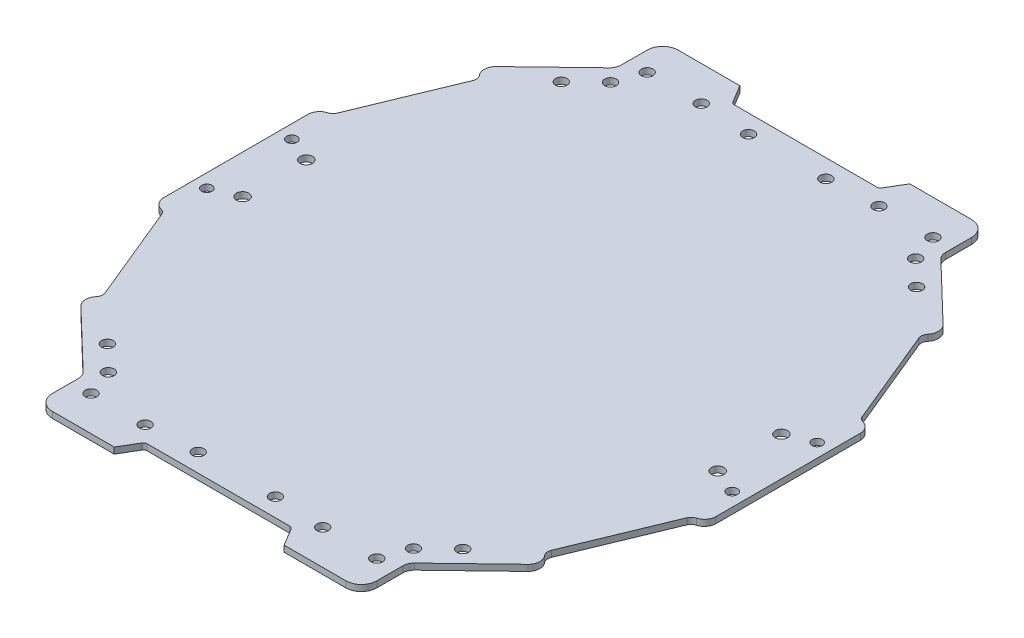
SolidWorks part; units mm, degrees
ref_plane "Front Plane" through (0, 0, 0) normal (0, 0, 1) x (1, 0, 0)
ref_plane "Top Plane" through (0, 0, 0) normal (0, 1, 0) x (1, 0, 0)
ref_plane "Right Plane" through (0, 0, 0) normal (1, 0, 0) x (0, 0, -1)
ref_plane "Plane1"
sketch "Sketch1" plane through (0, 0, 0) normal (0, 1, 0) x (-1, 0, 0)
  line L0 (59.7752, 259.0599) -> (56.7752, 264.0599)
  line L1 (56.7752, 264.0599) -> (36.7752, 264.0599)
  line L2 (36.7752, 264.0599) -> (36.7752, 252.0599)
  line L3 (36.7752, 252.0599) -> (18.7553, 234.7311)
  line L4 (18.7553, 234.7311) -> (21.5279, 231.8479)
  line L5 (21.5279, 231.8479) -> (10.2752, 204.5599)
  line L6 (10.2752, 204.5599) -> (7.2752, 204.5599)
  line L7 (7.2752, 204.5599) -> (7.2752, 183.0599)
  line L8 (7.2752, 183.0599) -> (7.2752, 161.5599)
  line L9 (7.2752, 161.5599) -> (10.2752, 161.5599)
  line L10 (10.2752, 161.5599) -> (21.5279, 134.2718)
  line L11 (21.5279, 134.2718) -> (18.7553, 131.3886)
  line L12 (18.7553, 131.3886) -> (36.7752, 114.0599)
  line L13 (36.7752, 114.0599) -> (36.7752, 102.0599)
  line L14 (36.7752, 102.0599) -> (56.7752, 102.0599)
  line L15 (56.7752, 102.0599) -> (59.7752, 107.0599)
  line L16 (59.7752, 107.0599) -> (78.7752, 107.0599)
  line L17 (78.7752, 107.0599) -> (97.7752, 107.0599)
  line L18 (97.7752, 107.0599) -> (100.7752, 102.0599)
  line L19 (100.7752, 102.0599) -> (120.7752, 102.0599)
  line L20 (120.7752, 102.0599) -> (120.7752, 114.0599)
  line L21 (120.7752, 114.0599) -> (138.795, 131.3886)
  line L22 (138.795, 131.3886) -> (136.0224, 134.2718)
  line L23 (136.0224, 134.2718) -> (147.2752, 161.5599)
  line L24 (147.2752, 161.5599) -> (150.2752, 161.5599)
  line L25 (150.2752, 161.5599) -> (150.2752, 183.0599)
  line L26 (150.2752, 183.0599) -> (150.2752, 204.5599)
  line L27 (150.2752, 204.5599) -> (147.2752, 204.5599)
  line L28 (147.2752, 204.5599) -> (136.0224, 231.8479)
  line L29 (136.0224, 231.8479) -> (138.795, 234.7311)
  line L30 (138.795, 234.7311) -> (120.7752, 252.0599)
  line L31 (120.7752, 252.0599) -> (120.7752, 264.0599)
  line L32 (120.7752, 264.0599) -> (100.7752, 264.0599)
  line L33 (100.7752, 264.0599) -> (97.7752, 259.0599)
  line L34 (97.7752, 259.0599) -> (78.7752, 259.0599)
  line L35 (78.7752, 259.0599) -> (59.7752, 259.0599)
  line L37 (2.8032, 179.0599) -> (-51.2357, 179.0599)
  line L38 (78.7752, 259.0599) -> (78.7752, 107.0599) construction
  line L39 (150.2752, 183.0599) -> (7.2752, 183.0599) construction
  line L40 (2.8032, 179.0599) -> (2.8032, 183.0599)
  line L41 (2.8032, 183.0599) -> (-51.2357, 183.0599)
  line L42 (-51.2357, 179.0599) -> (-51.2357, 183.0599)
  line L43 (2.8032, 179.0599) -> (-51.2357, 183.0599) construction
  line L44 (2.8032, 183.0599) -> (-51.2357, 179.0599) construction
  line L85 (91.8838, 199.6325) -> (91.9874, 199.5289)
  line L87 (95.3777, 196.1387) -> (95.4193, 196.097)
  circle A0 centre (55.7752, 111.0599) radius 1.5
  circle A1 centre (39.2752, 118.0599) radius 1.5
  circle A4 centre (17.2752, 174.8099) radius 1.6
  circle A22 centre (41.7752, 255.0599) radius 1.5
  circle A23 centre (39.2752, 248.0599) radius 1.5
  circle A24 centre (10.7752, 194.0599) radius 1.35
  circle A25 centre (88.7752, 111.8099) radius 1.5
  circle A27 centre (115.7752, 111.0599) radius 1.5
  circle A28 centre (118.2752, 118.0599) radius 1.5
  circle A29 centre (140.2752, 174.8099) radius 1.6
  circle A30 centre (115.7752, 255.0599) radius 1.5
  circle A31 centre (88.7752, 254.3099) radius 1.5
  circle A32 centre (140.2752, 191.3099) radius 1.6
  circle A33 centre (146.7752, 194.0599) radius 1.35
  circle A53 centre (101.7752, 255.0599) radius 1.5
  circle A54 centre (118.2752, 248.0599) radius 1.5
  circle A55 centre (146.7752, 172.0599) radius 1.35
  circle A57 centre (101.7752, 111.0599) radius 1.5
  circle A69 centre (17.2752, 191.3099) radius 1.6
  circle A71 centre (55.7752, 255.0599) radius 1.5
  circle A73 centre (68.7752, 254.3099) radius 1.5
  circle A74 centre (10.7752, 172.0599) radius 1.35
  circle A76 centre (68.7752, 111.8099) radius 1.5
  circle A77 centre (41.7752, 111.0599) radius 1.5
  circle A82 centre (32.7752, 124.3099) radius 1.5
  circle A86 centre (124.7752, 241.8099) radius 1.5
  circle A87 centre (32.7752, 241.8099) radius 1.5
  circle A91 centre (124.7752, 124.3099) radius 1.5
  point P40 (-24.2162, 181.0599)
  point P41 (150.2752, 193.8099)
  point P48 (0, 0)
  dimension "D1" = 143
  dimension "D2" = 162
extrude "Extrusion1" add sketch "Sketch1" along normal blind 1.6
fillet "Fillet1" radius 1 4 edges at (-97.7752, 0.8, 107.0599) (-59.7752, 0.8, 107.0599) (-59.7752, 0.8, 259.0599) (-97.7752, 0.8, 259.0599)
fillet "Fillet2" radius 4 4 edges at (-120.7752, 0.8, 102.0599) (-36.7752, 0.8, 102.0599) (-120.7752, 0.8, 264.0599) (-36.7752, 0.8, 264.0599)
fillet "Fillet3" radius 3 4 edges at (-120.7752, 0.8, 114.0599) (-36.7752, 0.8, 114.0599) (-36.7752, 0.8, 252.0599) (-120.7752, 0.8, 252.0599)
fillet "Fillet4" radius 3 1 edges at (-138.795, 0.8, 234.7311)
fillet "Fillet5" radius 2 1 edges at (-136.0224, 0.8, 231.8479)
fillet "Fillet6" radius 2 1 edges at (-21.5279, 0.8, 231.8479)
fillet "Fillet7" radius 3 1 edges at (-18.7553, 0.8, 234.7311)
fillet "Fillet8" radius 3 2 edges at (-138.795, 0.8, 131.3886) (-18.7553, 0.8, 131.3886)
fillet "Fillet9" radius 2 2 edges at (-21.5279, 0.8, 134.2718) (-136.0224, 0.8, 134.2718)
fillet "Fillet10" radius 2 4 edges at (-10.2752, 0.8, 161.5599) (-10.2752, 0.8, 204.5599) (-147.2752, 0.8, 204.5599) (-147.2752, 0.8, 161.5599)
fillet "Fillet11" radius 3 4 edges at (-150.2752, 0.8, 161.5599) (-150.2752, 0.8, 204.5599) (-7.2752, 0.8, 204.5599) (-7.2752, 0.8, 161.5599)
